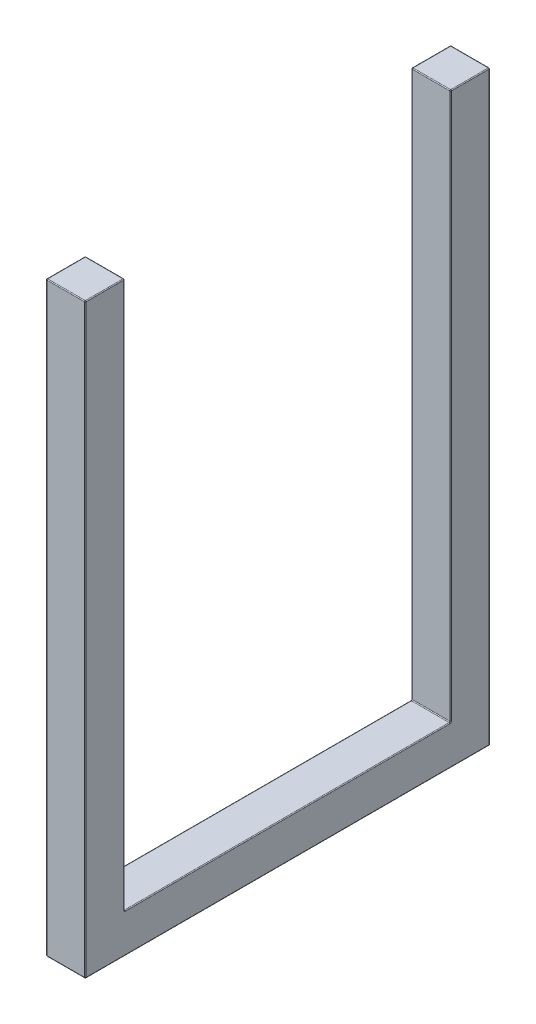
SolidWorks part; units mm, degrees
material "1023 Carbon Steel Sheet (SS)"
ref_plane "Front Plane" through (0, 0, 0) normal (0, 0, 1) x (1, 0, 0)
ref_plane "Top Plane" through (0, 0, 0) normal (0, 1, 0) x (1, 0, 0)
ref_plane "Right Plane" through (0, 0, 0) normal (1, 0, 0) x (0, 0, -1)
sketch "Sketch1" plane through (0, 0, 0) normal (0, 1, 0) x (1, 0, 0)
  line L0 (0, 0) -> (0, 98.17) construction
  line L1 (-457.2, 254) -> (-407.9875, 254)
  line L2 (-457.2, 254) -> (-457.2, 204.7875)
  line L3 (-457.2, 204.7875) -> (-407.9875, 204.7875)
  line L4 (-407.9875, 254) -> (-407.9875, 204.7875)
  line L9 (0, 0) -> (-57.4998, 0) construction
  line L10 (-407.9875, -254) -> (-407.9875, -204.7875)
  line L11 (-457.2, -204.7875) -> (-407.9875, -204.7875)
  line L12 (-457.2, -254) -> (-457.2, -204.7875)
  line L13 (-457.2, -254) -> (-407.9875, -254)
  dimension "D1" = 49.2125
  dimension "D2" = 49.2125
  dimension "D3" = 407.9875
  dimension "D4" = 409.575
extrude "Boss-Extrude1" add sketch "Sketch1" along normal blind 736.6
sketch "Sketch2" plane through (0, 0, -204.7875) normal (0, 0, 1) x (1, 0, 0)
  line L0 (-457.2, 736.6) -> (-457.2, 0) construction
  line L1 (-407.9875, 0) -> (-457.2, 0)
  line L2 (-407.9875, 0) -> (-407.9875, 49.2125)
  line L3 (-407.9875, 49.2125) -> (-457.2, 49.2125)
  line L4 (-457.2, 0) -> (-457.2, 49.2125)
extrude "Boss-Extrude2" add sketch "Sketch2" along normal up to next (458.7875 mm away)
fillet "Fillet1" radius 1.016 24 edges at (-432.5938, 736.6, -204.7875) (-432.5938, 736.6, 204.7875) (-457.2, 736.6, -229.3937) (-457.2, 392.9062, -204.7875) (-457.2, 392.9062, 204.7875) (-457.2, 736.6, 229.3937) (-457.2, 0, 0) (-432.5938, 736.6, -254) (-457.2, 368.3, -254) (-432.5938, 0, -254) (-457.2, 49.2125, 0) (-432.5938, 49.2125, -204.7875) (-432.5938, 49.2125, 204.7875) (-407.9875, 736.6, 229.3937) (-407.9875, 392.9062, 204.7875) (-407.9875, 49.2125, 0) (-407.9875, 392.9062, -204.7875) (-407.9875, 736.6, -229.3937) (-407.9875, 368.3, -254) (-407.9875, 0, 0) (-457.2, 368.3, 254) (-432.5938, 736.6, 254) (-407.9875, 368.3, 254) (-432.5938, 0, 254)
